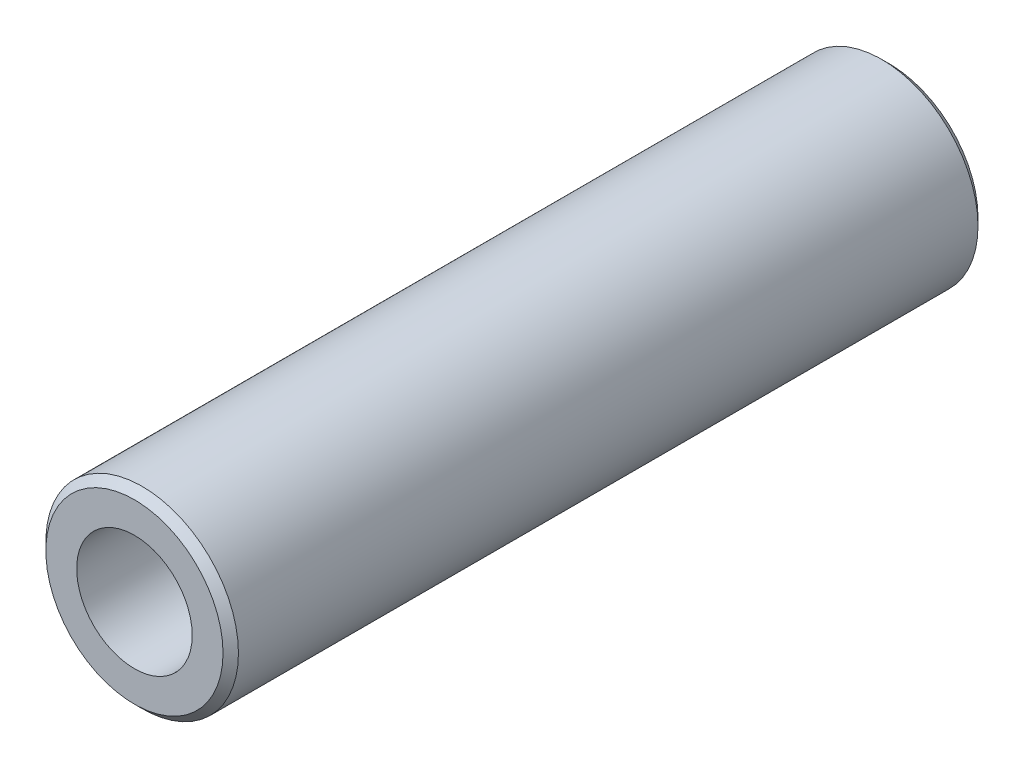
SolidWorks part; units mm, degrees
ref_plane "Front Plane" through (0, 0, 0) normal (0, 0, 1) x (1, 0, 0)
ref_plane "Top Plane" through (0, 0, 0) normal (0, 1, 0) x (1, 0, 0)
ref_plane "Right Plane" through (0, 0, 0) normal (1, 0, 0) x (0, 0, -1)
sketch "Sketch2" plane through (0, 0, 0) normal (0, 0, 1) x (1, 0, 0)
  circle A0 centre (0, 0) radius 6.25
  dimension "D1" = 12.5
extrude "Extrude-Thin1" add sketch "Sketch2" along normal mid plane 49 thin thin type one direction reverse wall 2.5
chamfer "Chamfer1" distance 0.5 angle 45 2 edges at (6.25, 0, -24.5) (6.25, 0, 24.5)
